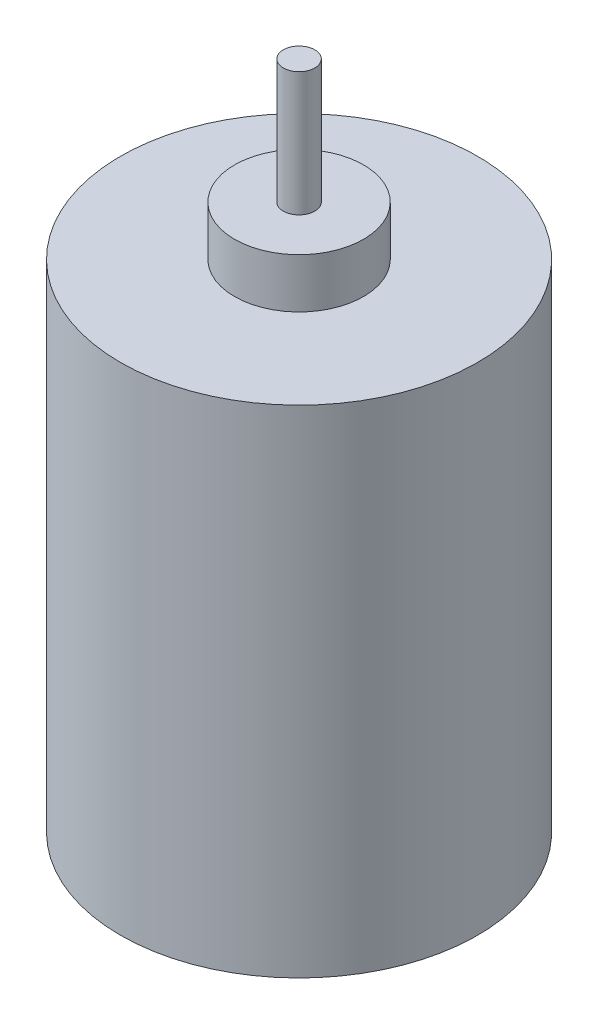
SolidWorks part; units mm, degrees
ref_plane "Front Plane" through (0, 0, 0) normal (0, 0, 1) x (1, 0, 0)
ref_plane "Top Plane" through (0, 0, 0) normal (0, 1, 0) x (1, 0, 0)
ref_plane "Right Plane" through (0, 0, 0) normal (1, 0, 0) x (0, 0, -1)
sketch "Sketch1" plane through (0, 0, 0) normal (0, 1, 0) x (1, 0, 0)
  circle A0 centre (0, 0) radius 18
  dimension "D1" = 36
extrude "Boss-Extrude1" add sketch "Sketch1" along normal blind 50
sketch "Sketch2" plane through (0, 0, 0) normal (0, 1, 0) x (1, 0, 0)
  circle A0 centre (0, 0) radius 6.5
  dimension "D1" = 13
extrude "Boss-Extrude2" add sketch "Sketch2" along normal blind 5 from surface at 50 starting at face at (0, 50, 18)
sketch "Sketch3" plane through (0, 0, 0) normal (0, 1, 0) x (1, 0, 0)
  circle A0 centre (0, 0) radius 1.5875
  dimension "D1" = 3.175
extrude "Boss-Extrude3" add sketch "Sketch3" along normal blind 12.5 from surface at 55 starting at face at (0, 55, 6.5)
